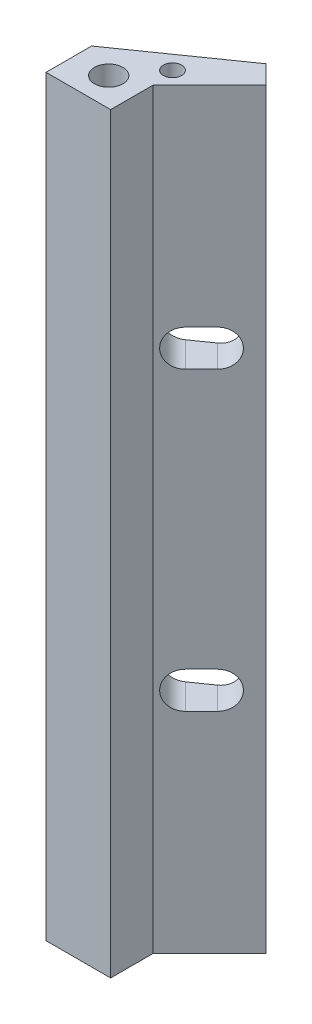
SolidWorks part; units mm, degrees
ref_plane "Front Plane" through (0, 0, 0) normal (0, 0, 1) x (1, 0, 0)
ref_plane "Top Plane" through (0, 0, 0) normal (0, 1, 0) x (1, 0, 0)
ref_plane "Right Plane" through (0, 0, 0) normal (1, 0, 0) x (0, 0, -1)
ref_plane "Plane1" through (0, 66, 0) normal (0, 1, 0) x (1, 0, 0)
sketch "Sketch1" plane through (0, 66, 0) normal (0, 1, 0) x (1, 0, 0)
  line L0 (3, 0.7019) -> (-6, -5.6)
  line L1 (-6, -5.6) -> (-6, -9.6)
  line L2 (-6, -9.6) -> (-0.331, -9.6)
  line L3 (-0.331, -9.6) -> (-0.331, -5.8666)
  line L4 (-0.331, -5.8666) -> (4.6187, -0.9168)
  line L5 (4.6187, -0.9168) -> (3, 0.7019)
extrude "Boss-Extrude1" add sketch "Sketch1" against normal blind 66
sketch "Sketch2" plane through (2.7678, 0, 2.7678) normal (0.7071, 0, 0.7071) x (0.7071, 0, -0.7071)
  line L0 (-0.3824, 47.6) -> (-2.3824, 47.6)
  line L1 (-2.3824, 44.4) -> (-0.3824, 44.4)
  arc A0 (-2.3824, 47.6) -> (-2.3824, 44.4) centre (-2.3824, 46) ccw
  arc A1 (-0.3824, 44.4) -> (-0.3824, 47.6) centre (-0.3824, 46) ccw
extrude "Cut-Extrude1" cut sketch "Sketch2" against normal through all
sketch "Sketch3" plane through (2.7678, 0, 2.7678) normal (0.7071, 0, 0.7071) x (0.7071, 0, -0.7071)
  line L0 (-0.3824, 21.6) -> (-2.3824, 21.6)
  line L1 (-2.3824, 18.4) -> (-0.3824, 18.4)
  arc A0 (-2.3824, 21.6) -> (-2.3824, 18.4) centre (-2.3824, 20) ccw
  arc A1 (-0.3824, 18.4) -> (-0.3824, 21.6) centre (-0.3824, 20) ccw
extrude "Cut-Extrude2" cut sketch "Sketch3" against normal up to next
hole_wizard "Ø2.5 (2.5) Diameter Hole1" positions "Sketch5" profile "Sketch4" hole size "Ø2.5" standard "ANSI Metric"
sketch "Sketch5" plane through (0, 0, 0) normal (0, -1, 0) x (-1, 0, 0)
  point P0 (3, -7.1)
sketch "Sketch4" plane through (-3, 0, 7.1) normal (1, 0, 0) x (0, 0, -1)
  line L0 (0, 0) -> (0, 8.7511)
  line L1 (0, 8.7511) -> (1.25, 8)
  line L2 (1.25, 8) -> (1.25, 0)
  line L5 (1.25, 0) -> (0, 0)
  line L10 (0, 8.7511) -> (-1.25, 8) construction
  line L11 (0, -6.35) -> (0, 107.95) construction
  dimension "Hole Dia." = 2.5
  dimension "Hole Depth" = 8
  dimension "Drill Angle" = 118
hole_wizard "Tap Drill for M2x0.4 Tap1" positions "Sketch7" profile "Sketch6" hole size "M2x0.4" standard "ANSI Metric"
sketch "Sketch7" plane through (0, 0, 0) normal (0, -1, 0) x (-1, 0, 0)
  point P0 (0.604, -3.897)
sketch "Sketch6" plane through (-0.604, 0, 3.897) normal (1, 0, 0) x (0, 0, -1)
  line L0 (0, 0) -> (0, 8.4807)
  line L1 (0, 8.4807) -> (0.8, 8)
  line L2 (0.8, 8) -> (0.8, 0)
  line L5 (0.8, 0) -> (0, 0)
  line L10 (0, 8.4807) -> (-0.8, 8) construction
  line L11 (0, -6.35) -> (0, 107.95) construction
  dimension "Hole Dia." = 1.6
  dimension "Hole Depth" = 8
  dimension "Drill Angle" = 118
hole_wizard "Ø2.5 (2.5) Diameter Hole2" positions "Sketch9" profile "Sketch8" hole size "Ø2.5" standard "ANSI Metric"
sketch "Sketch9" plane through (0, 66, 0) normal (0, 1, 0) x (1, 0, 0)
  point P0 (-3, -7.1)
sketch "Sketch8" plane through (-3, 66, 7.1) normal (1, 0, 0) x (0, 0, 1)
  line L0 (0, 0) -> (0, 8.7511)
  line L1 (0, 8.7511) -> (1.25, 8)
  line L2 (1.25, 8) -> (1.25, 0)
  line L5 (1.25, 0) -> (0, 0)
  line L10 (0, 8.7511) -> (-1.25, 8) construction
  line L11 (0, -6.35) -> (0, 107.95) construction
  dimension "Hole Dia." = 2.5
  dimension "Hole Depth" = 8
  dimension "Drill Angle" = 118
hole_wizard "Tap Drill for M2x0.4 Tap2" positions "Sketch11" profile "Sketch10" hole size "M2x0.4" standard "ANSI Metric"
sketch "Sketch11" plane through (0, 66, 0) normal (0, 1, 0) x (1, 0, 0)
  point P0 (-0.604, -3.897)
sketch "Sketch10" plane through (-0.604, 66, 3.897) normal (1, 0, 0) x (0, 0, 1)
  line L0 (0, 0) -> (0, 8.4807)
  line L1 (0, 8.4807) -> (0.8, 8)
  line L2 (0.8, 8) -> (0.8, 0)
  line L5 (0.8, 0) -> (0, 0)
  line L10 (0, 8.4807) -> (-0.8, 8) construction
  line L11 (0, -6.35) -> (0, 107.95) construction
  dimension "Hole Dia." = 1.6
  dimension "Hole Depth" = 8
  dimension "Drill Angle" = 118
